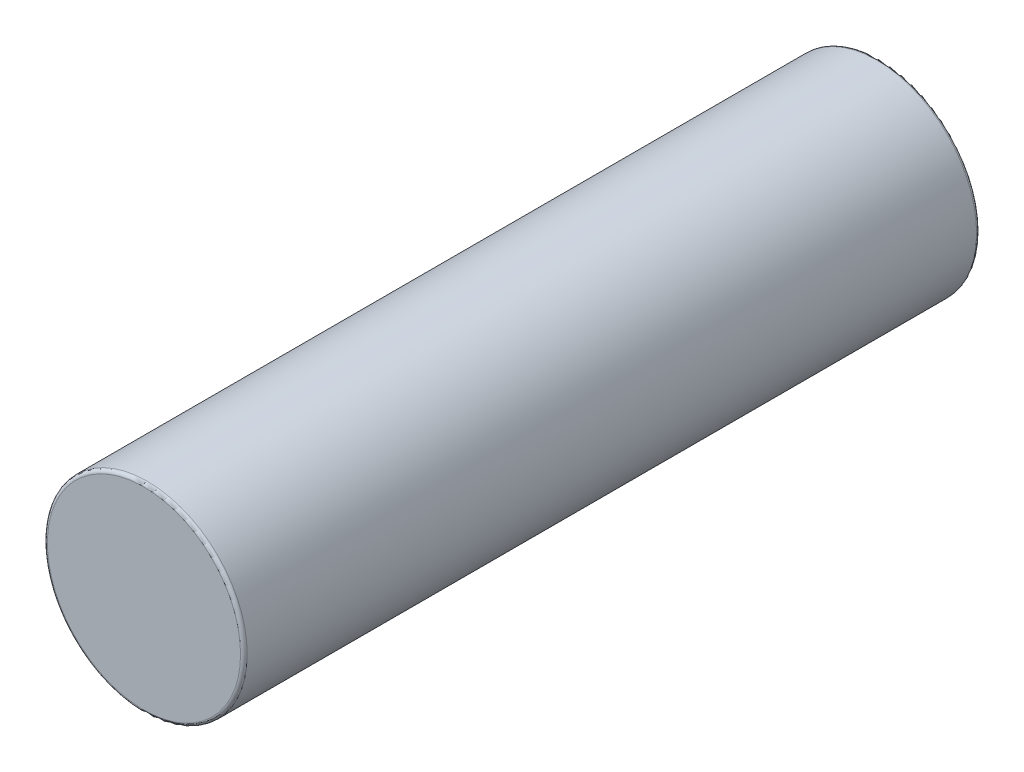
SolidWorks part; units mm, degrees
ref_plane "Front Plane" through (0, 0, 0) normal (0, 0, 1) x (1, 0, 0)
ref_plane "Top Plane" through (0, 0, 0) normal (0, 1, 0) x (1, 0, 0)
ref_plane "Right Plane" through (0, 0, 0) normal (1, 0, 0) x (0, 0, -1)
sketch "Sketch1" plane through (0, 0, 0) normal (0, 0, 1) x (1, 0, 0)
  circle A0 centre (0, 0) radius 7.5
  dimension "D1" = 15
extrude "Boss-Extrude1" add sketch "Sketch1" along normal blind 55.25
fillet "Fillet1" radius 0.25 2 edges at (7.5, 0, 0) (7.5, 0, 55.25)
